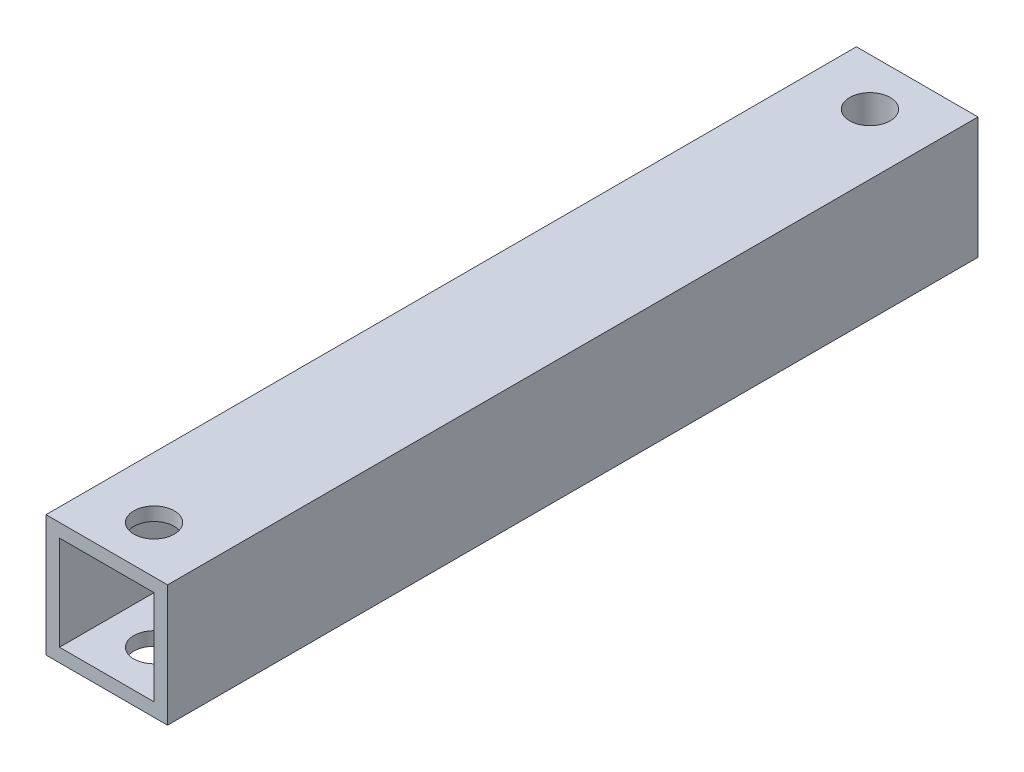
SolidWorks part; units mm, degrees
ref_plane "正面" through (0, 0, 0) normal (0, 0, 1) x (1, 0, 0)
ref_plane "平面" through (0, 0, 0) normal (0, 1, 0) x (1, 0, 0)
ref_plane "右側面" through (0, 0, 0) normal (1, 0, 0) x (0, 0, -1)
sketch "ｽｹｯﾁ1" plane through (0, 0, 0) normal (0, 0, 1) x (1, 0, 0)
  line L1 (-4.5, 4.5) -> (4.5, 4.5)
  line L2 (-4.5, 4.5) -> (-4.5, -4.5)
  line L3 (-4.5, -4.5) -> (4.5, -4.5)
  line L4 (4.5, 4.5) -> (4.5, -4.5)
  line L5 (-4.5, 4.5) -> (4.5, -4.5) construction
  line L6 (-4.5, -4.5) -> (4.5, 4.5) construction
  point P0 (0, 0)
  dimension "D1" = 9
  dimension "D2" = 9
extrude "ﾎﾞｽ - 押し出し1" add sketch "ｽｹｯﾁ1" along normal blind 60
sketch "ｽｹｯﾁ2" plane through (0, 0, 60) normal (0, 0, 1) x (1, 0, 0)
  line L1 (-3.5, 3.5) -> (3.5, 3.5)
  line L2 (-3.5, 3.5) -> (-3.5, -3.5)
  line L3 (-3.5, -3.5) -> (3.5, -3.5)
  line L4 (3.5, 3.5) -> (3.5, -3.5)
  line L5 (-3.5, 3.5) -> (3.5, -3.5) construction
  line L6 (-3.5, -3.5) -> (3.5, 3.5) construction
  point P0 (0, 0)
  dimension "D1" = 7
  dimension "D2" = 7
extrude "ｶｯﾄ - 押し出し1" cut sketch "ｽｹｯﾁ2" against normal blind 56
sketch "ｽｹｯﾁ3" plane through (0, 4.5, 0) normal (0, 1, 0) x (1, 0, 0)
  line L0 (0, 0) -> (0, -3.5)
  line L1 (0, -60) -> (0, -56.5)
  line L2 (4.5, -60) -> (-4.5, -60) construction
  circle A0 centre (0, -3.5) radius 1.5
  circle A1 centre (0, -56.5) radius 1.5
  dimension "D1" = 3
  dimension "D2" = 3
  dimension "D3" = 3.5
  dimension "D4" = 3.5
extrude "ｶｯﾄ - 押し出し2" cut sketch "ｽｹｯﾁ3" against normal blind 56
